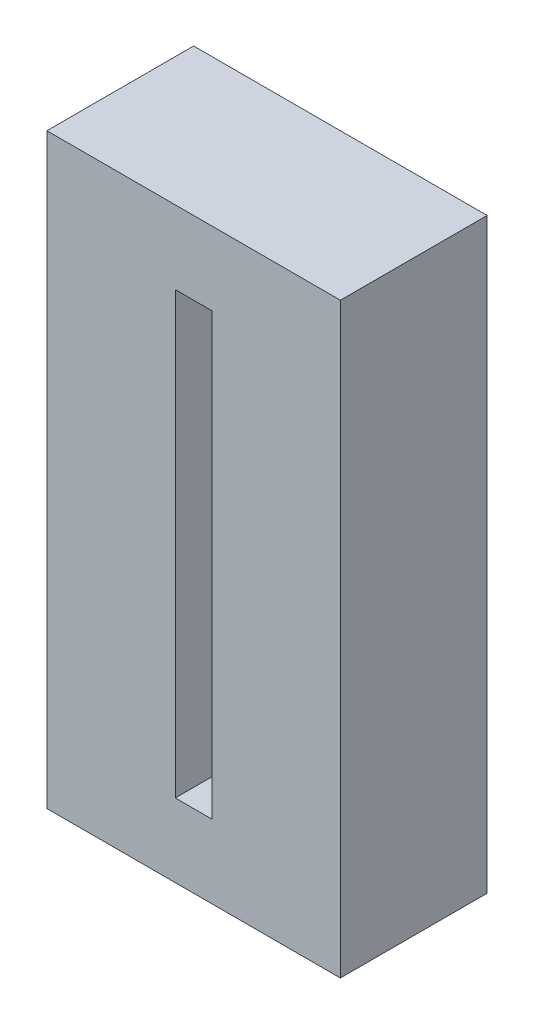
SolidWorks part; units mm, degrees
ref_plane "Front Plane" through (0, 0, 0) normal (0, 0, 1) x (1, 0, 0)
ref_plane "Top Plane" through (0, 0, 0) normal (0, 1, 0) x (1, 0, 0)
ref_plane "Right Plane" through (0, 0, 0) normal (1, 0, 0) x (0, 0, -1)
sketch "Sketch1" plane through (0, 0, 0) normal (0, 0, 1) x (1, 0, 0)
  line L1 (0, 0) -> (101.6, 0)
  line L2 (0, 0) -> (0, 203.2)
  line L3 (0, 203.2) -> (101.6, 203.2)
  line L4 (101.6, 0) -> (101.6, 203.2)
  line L5 (44.45, 25.4) -> (57.15, 25.4)
  line L6 (44.45, 25.4) -> (44.45, 177.8)
  line L7 (44.45, 177.8) -> (57.15, 177.8)
  line L8 (57.15, 25.4) -> (57.15, 177.8)
  dimension "D1" = 101.6
  dimension "D2" = 203.2
  dimension "D3" = 25.4
  dimension "D4" = 152.4
  dimension "D5" = 44.45
  dimension "D6" = 44.45
extrude "Boss-Extrude1" add sketch "Sketch1" along normal blind 50.8
